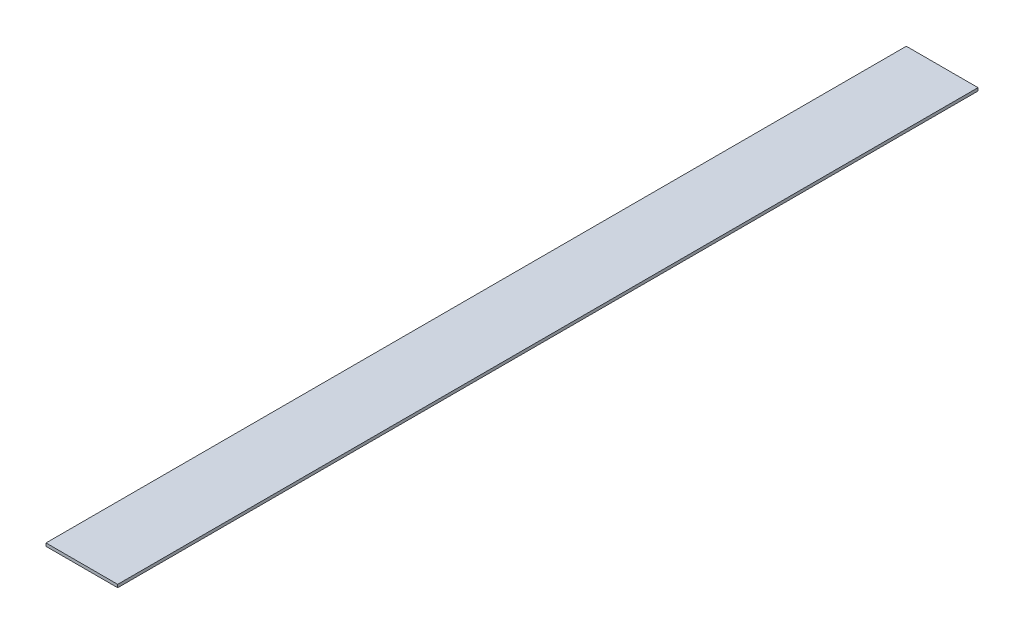
SolidWorks part; units mm, degrees
ref_plane "Front Plane" through (0, 0, 0) normal (0, 0, 1) x (1, 0, 0)
ref_plane "Top Plane" through (0, 0, 0) normal (0, 1, 0) x (1, 0, 0)
ref_plane "Right Plane" through (0, 0, 0) normal (1, 0, 0) x (0, 0, -1)
sketch "Sketch1" plane through (0, 0, 0) normal (0, 1, 0) x (1, 0, 0)
  line L1 (0, 0) -> (76.2, 0)
  line L2 (0, 0) -> (0, 914.4)
  line L3 (0, 914.4) -> (76.2, 914.4)
  line L4 (76.2, 0) -> (76.2, 914.4)
  dimension "D1" = 914.4
  dimension "D2" = 76.2
extrude "Boss-Extrude1" add sketch "Sketch1" along normal blind 3.175
